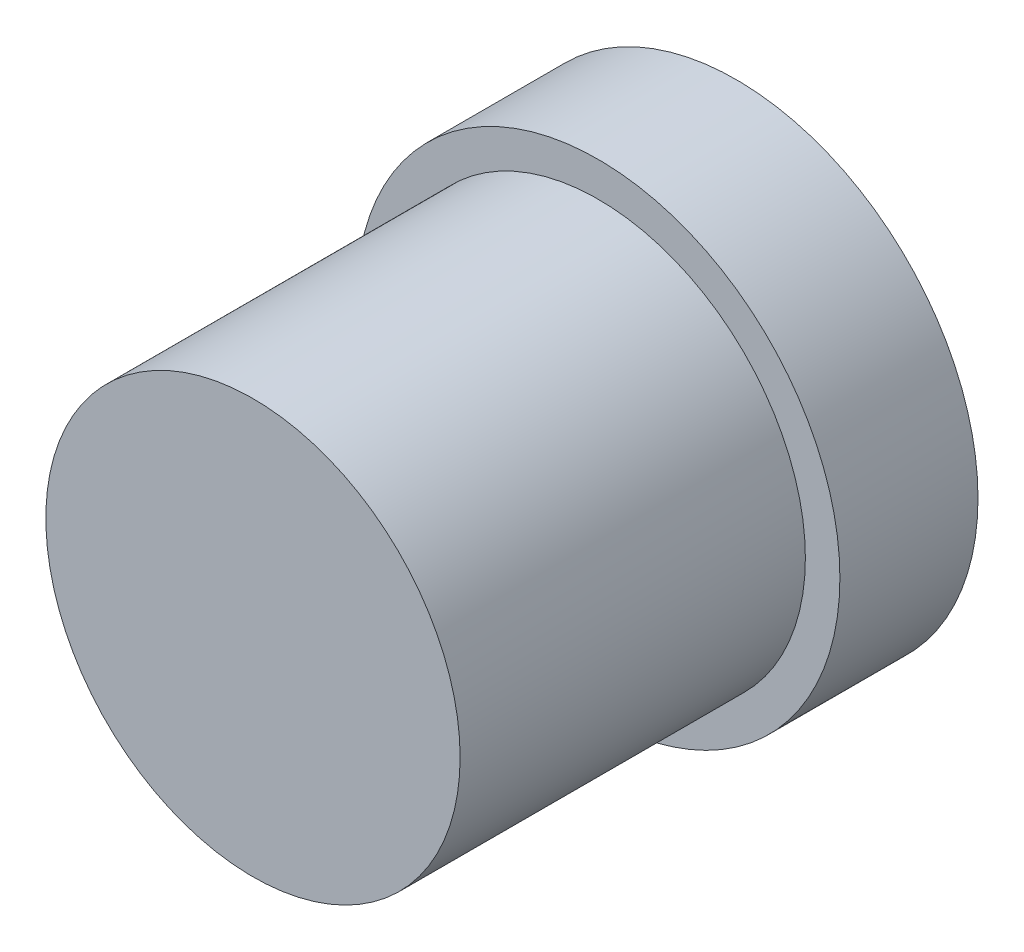
SolidWorks part; units mm, degrees
ref_plane "Front Plane" through (0, 0, 0) normal (0, 0, 1) x (1, 0, 0)
ref_plane "Top Plane" through (0, 0, 0) normal (0, 1, 0) x (1, 0, 0)
ref_plane "Right Plane" through (0, 0, 0) normal (1, 0, 0) x (0, 0, -1)
sketch "Sketch1" plane through (0, 0, 0) normal (0, 0, 1) x (1, 0, 0)
  circle A0 centre (0, 0) radius 7
  dimension "D1" = 14
extrude "Boss-Extrude1" add sketch "Sketch1" along normal blind 4
sketch "Sketch2" plane through (0, 0, 4) normal (0, 0, 1) x (1, 0, 0)
  circle A0 centre (0, 0) radius 6
  dimension "D1" = 12
extrude "Boss-Extrude2" add sketch "Sketch2" along normal blind 10
